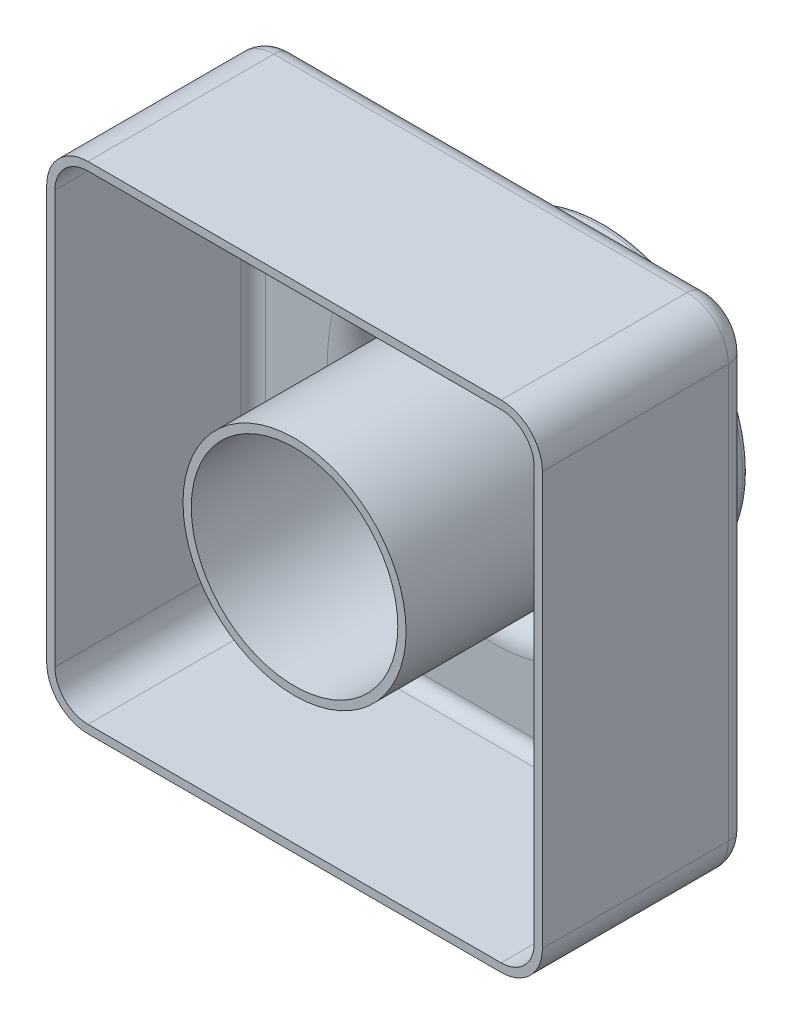
SolidWorks part; units mm, degrees
ref_plane "Front Plane" through (0, 0, 0) normal (0, 0, 1) x (1, 0, 0)
ref_plane "Top Plane" through (0, 0, 0) normal (0, 1, 0) x (1, 0, 0)
ref_plane "Right Plane" through (0, 0, 0) normal (1, 0, 0) x (0, 0, -1)
sketch "Sketch3" plane through (0, 0, 0) normal (0, 0, 1) x (1, 0, 0)
  line L1 (0, 0) -> (120, 0)
  line L2 (0, 0) -> (0, -120)
  line L3 (0, -120) -> (120, -120)
  line L4 (120, 0) -> (120, -120)
  dimension "D1" = 120
  dimension "D2" = 120
extrude "Boss-Extrude2" add sketch "Sketch3" along normal blind 50
sketch "Sketch6" plane through (0, 0, 0) normal (0, 0, -1) x (-1, 0, 0)
  line L0 (-120, 0) -> (0, 0) construction
  line L2 (0, 0) -> (0, -120) construction
  circle A0 centre (-60, -60) radius 35
  point P6 (-150.09, -13.3928)
  dimension "D1" = 70
  dimension "D3" = 60
  dimension "D2" = 60
extrude "Boss-Extrude3" add sketch "Sketch6" along normal blind 25
sketch "Sketch8" plane through (0, 0, -25) normal (0, 0, -1) x (-1, 0, 0)
  circle A0 centre (-60, -60) radius 25
  dimension "D1" = 50
extrude "Cut-Extrude1" cut sketch "Sketch8" against normal blind 80
fillet "Fillet1" radius 1.5 2 edges at (25, -60, -25) (35, -60, -25)
fillet "Fillet2" radius 10 4 edges at (0, 0, 25) (120, 0, 25) (120, -120, 25) (0, -120, 25)
fillet "Fillet3" radius 5 9 edges at (25, -60, 0) (117.0711, -2.9289, 0) (60, 0, 0) (2.9289, -2.9289, 0) (0, -60, 0) (2.9289, -117.0711, 0) (60, -120, 0) (117.0711, -117.0711, 0) (120, -60, 0)
shell "Shell1" thickness 2
